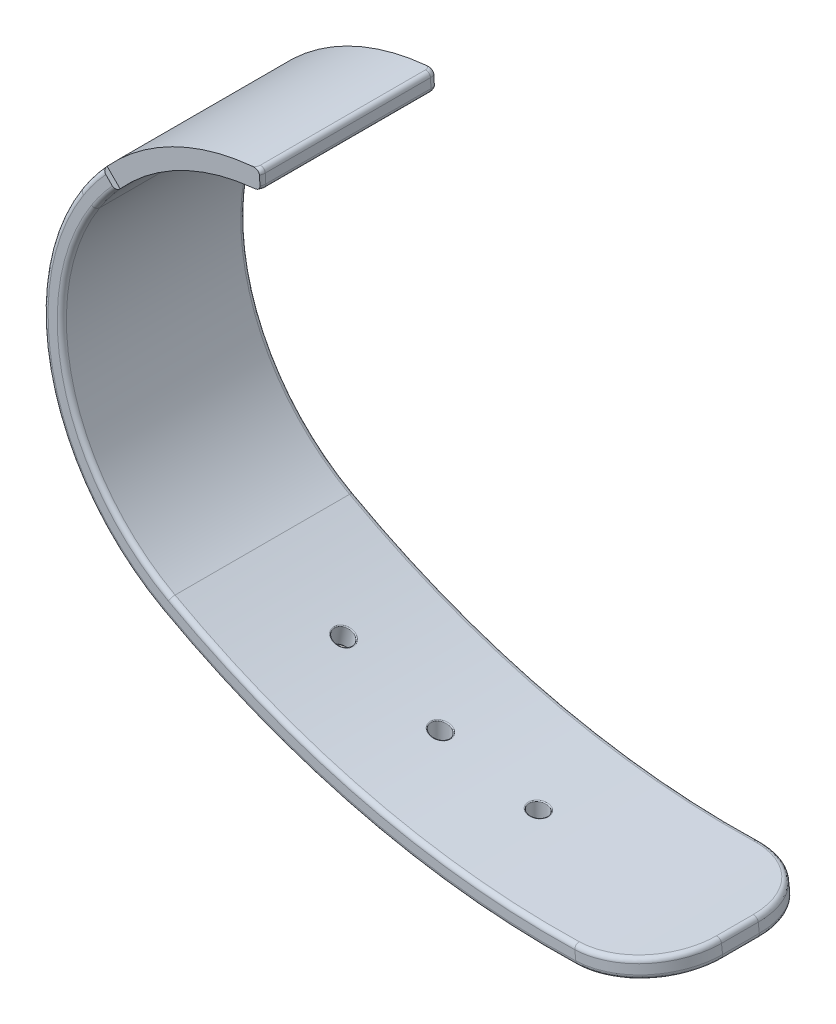
SolidWorks part; units mm, degrees
ref_plane "Face" through (0, 0, 0) normal (0, 0, 1) x (1, 0, 0)
ref_plane "Dessus" through (0, 0, 0) normal (0, 1, 0) x (1, 0, 0)
ref_plane "Droite" through (0, 0, 0) normal (1, 0, 0) x (0, 0, -1)
sketch "Esquisse1" plane through (0, 0, 0) normal (0, 0, 1) x (1, 0, 0)
  arc A0 (-17.6021, -10.2793) -> (-9.4072, -42.7293) centre (1.6495, -22.6773) ccw
  arc A1 (-9.4072, -42.7293) -> (42.5588, -52.8351) centre (32.2505, 32.8196) ccw
  arc A2 (0, 0) -> (-17.6021, -10.2793) centre (1.3146, -22.4616) ccw
  dimension "D1" = 22.5
extrude "Extru.-Mince1" add sketch "Esquisse1" along normal mid plane 20 thin
fillet "Congé10" radius 8 2 edges at (42.6783, -53.828, 10) (42.6783, -53.828, -10)
fillet "Congé8" radius 1 2 edges at (-0.0584, 0.9983, 10) (-0.0584, 0.9983, -10)
sketch "Esquisse4" plane through (0, 0, 0) normal (0, 1, 0) x (1, 0, 0)
  line L0 (9.9696, 0) -> (24.7994, 0) construction
  line L1 (24.7994, 0) -> (42.5588, 0) construction
  line L2 (42.5588, -2) -> (42.5588, 2) construction
  line L3 (3.433, 0) -> (9.9696, 0) construction
  circle A0 centre (20.6543, 0) radius 1
  circle A1 centre (9.9696, 0) radius 1
  dimension "D1" = 2
extrude "Enlèv. mat.-Extru.4" cut sketch "Esquisse4" against normal through all
sketch "Esquisse5" plane through (0, 0, 0) normal (0, 1, 0) x (1, 0, 0)
  line L0 (0, -53.1867) -> (0, 55.6436) construction
ref_plane "Plan1" through (0, 0, 0) normal (0.1736, 0.9848, 0) x (0.9848, -0.1736, 0)
sketch "Esquisse6" plane through (0, 0, 0) normal (0.1736, 0.9848, 0) x (0.9848, -0.1736, 0)
  line L0 (0, 0) -> (7.5878, 0) construction
  line L1 (7.5878, 0) -> (17.5596, 0) construction
  circle A0 centre (7.5878, 0) radius 1
  spline S0 degree 3 poles (18.3242, -1) (18.7259, -1) (18.8571, -0.9751) (19.1048, -0.8771) (19.2186, -0.8046) (19.4106, -0.6212) (19.4887, -0.5097) (19.5941, -0.2665) (19.6221, -0.1326) (19.6221, 0.1326) (19.5943, 0.2662) (19.4883, 0.5106) (19.4109, 0.6211) (19.2166, 0.8063) (19.1029, 0.8781) (18.8555, 0.9754) (18.7225, 1.0002) (18.458, 0.9998) (18.3246, 0.9743) (18.0791, 0.8772) (17.9642, 0.8042) (17.7728, 0.622) (17.6941, 0.5106) (17.588, 0.2675) (17.5597, 0.1345) (17.5595, -0.1328) (17.5873, -0.2655) (17.694, -0.5108) (17.7722, -0.6215) (18.0603, -0.8958) (18.3242, -1) (18.7259, -1) (18.8571, -0.9751) knots -0.125 -0.125 0 0 0.0625 0.0625 0.125 0.125 0.1875 0.1875 0.25 0.25 0.3125 0.3125 0.375 0.375 0.4375 0.4375 0.5 0.5 0.5625 0.5625 0.625 0.625 0.6875 0.6875 0.75 0.75 0.8125 0.8125 0.875 0.875 1 1 1.0625 1.0625 1.125 only from (18.592, -1) to (18.592, -1) construction
  dimension "D1" = 2
extrude "Enlèv. mat.-Extru.5" cut sketch "Esquisse6" against normal through all
fillet "Congé11" radius 0.5 24 edges at (11.8686, -51.011, 10) (-20.5518, -28.284, 10) (-10.461, -3.289, 10) (-0.2187, -0.0139, 9.6247) (0, 0, 0) (-0.3747, -0.0251, -9.7811) (-10.461, -3.289, -10) (-20.5518, -28.284, -10) (11.8686, -51.011, -10) (40.8165, -53.0269, -6.9972) (42.5588, -52.8351, 0) (-0.4916, 1.9718, 9.7811) (-0.1169, 1.9966, 0) (-0.3355, 1.9828, -9.6247) (-11.4698, -1.5616, -10) (-22.4909, -28.7737, -10) (11.4866, -52.9764, -10) (39.8018, -55.1296, -8.2541) (42.7978, -54.8208, 0) (41.0555, -55.013, 6.9972) (11.4866, -52.9764, 10) (-22.4909, -28.7737, 10) (39.5623, -53.1428, 8.2544) (-11.4698, -1.5616, 10)
sketch "Esquisse7" plane through (0, 0, 10) normal (0, 0, 1) x (1, 0, 0)
  line L0 (-14.4761, -8.3202) -> (-18.5472, -4.2491)
  line L1 (-18.5472, -4.2491) -> (-4.3086, 9.9896)
  line L2 (-4.3086, 9.9896) -> (7.6145, -1.9335)
  line L3 (7.6145, -1.9335) -> (-14.4761, -8.3202)
extrude "Enlèv. mat.-Extru.6" cut sketch "Esquisse7" against normal blind 0.5
sketch "Esquisse8" plane through (0, 0, -10) normal (0, 0, -1) x (-1, 0, 0)
  line L4 (14.4761, -8.3202) -> (18.5472, -4.2491)
  line L5 (18.5472, -4.2491) -> (4.3086, 9.9896)
  line L6 (4.3086, 9.9896) -> (-7.6145, -1.9335)
  line L7 (-7.6145, -1.9335) -> (14.4761, -8.3202)
  line L8 (14.4761, -8.3202) -> (18.5472, -4.2491)
  line L9 (18.5472, -4.2491) -> (4.3086, 9.9896)
  line L10 (4.3086, 9.9896) -> (-7.6145, -1.9335)
  line L11 (-7.6145, -1.9335) -> (14.4761, -8.3202)
  dimension "D1" = 0
extrude "Enlèv. mat.-Extru.7" cut sketch "Esquisse8" against normal blind 0.5
fillet "Congé12" radius 0.1 6 edges at (0.3467, -47.3374, -0.2275) (9.7357, -50.4635, -0.9723) (20.4238, -52.6387, -0.9731) (-0.0078, -49.3479, -0.2276) (9.736, -52.5337, -0.9723) (20.4238, -54.6574, -0.9731)
